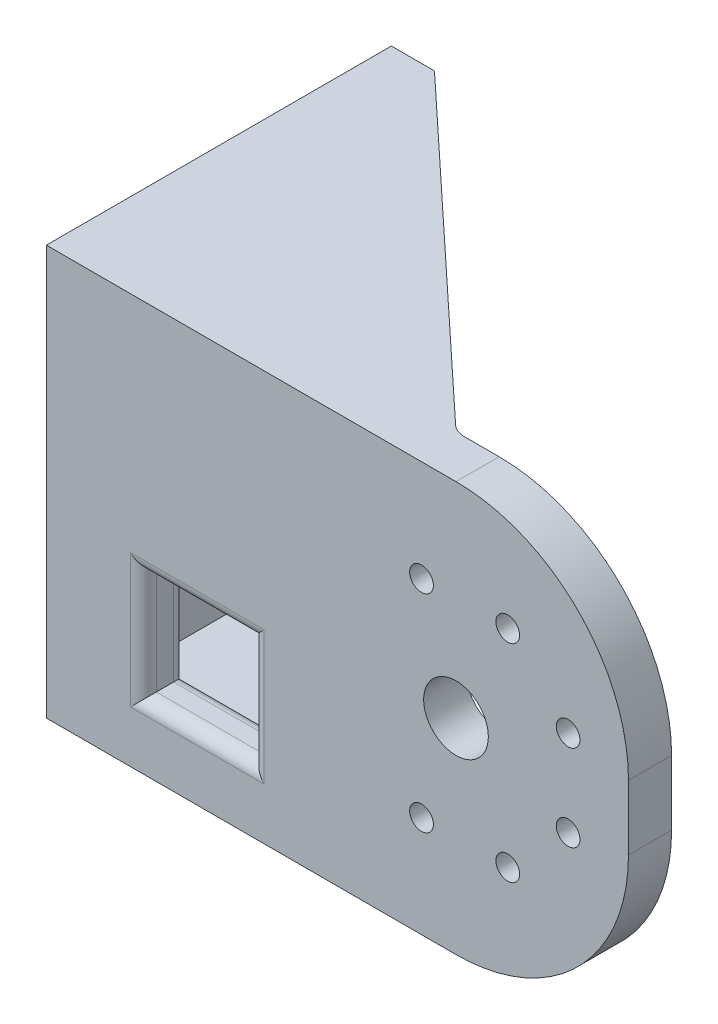
SolidWorks part; units mm, degrees
ref_plane "Front Plane" through (0, 0, 0) normal (0, 0, 1) x (1, 0, 0)
ref_plane "Top Plane" through (0, 0, 0) normal (0, 1, 0) x (1, 0, 0)
ref_plane "Right Plane" through (0, 0, 0) normal (1, 0, 0) x (0, 0, -1)
sketch "Sketch3" plane through (0, 0, 0) normal (0, 0, 1) x (1, 0, 0)
  line L6 (68.6171, 80.0599) -> (163.6171, 80.0599)
  line L10 (68.6171, 80.0599) -> (68.6171, -14.9401)
  line L36 (-101.4371, 49.8561) -> (-17.2351, 49.8561) construction
  line L70 (68.6171, -14.9401) -> (163.6171, -14.9401)
  line L71 (203.6171, 40.0599) -> (203.6171, 25.0599)
  circle A22 centre (163.6171, 32.5599) radius 7.5
  circle A23 centre (189.6171, 42.5599) radius 2.75
  circle A24 centre (155.6171, 56.5599) radius 2.75
  circle A25 centre (175.6171, 56.5599) radius 2.75
  circle A26 centre (155.6171, 8.5599) radius 2.75
  circle A27 centre (175.6171, 8.5599) radius 2.75
  circle A28 centre (189.6171, 22.5599) radius 2.75
  arc A29 (163.6171, -14.9401) -> (203.6171, 25.0599) centre (163.6171, 25.0599) ccw
  arc A30 (163.6171, 80.0599) -> (203.6171, 40.0599) centre (163.6171, 40.0599) cw
  point P23 (203.6171, 80.0599)
  dimension "D3" = 10
  dimension "D4" = 26
  dimension "D7" = 5.5
  dimension "D21" = 135
  dimension "D22" = 40
  dimension "D23" = 47.5
  dimension "D1" = 15
  dimension "D24" = 40
  dimension "D10" = 8
  dimension "D11" = 24
  dimension "D12" = 20
  dimension "D15" = 20
  dimension "D16" = 8
  dimension "D17" = 20
  dimension "D18" = 48
  dimension "D19" = 48
  dimension "D20" = 95
  dimension "D13" = 26
  dimension "D14" = 24
extrude "Boss-Extrude1" add sketch "Sketch3" along normal blind 10
sketch "Sketch4" plane through (0, 0, 0) normal (0, 0, -1) x (-1, 0, 0)
  line L0 (-68.6171, -14.9401) -> (-163.6171, -14.9401) construction
  line L1 (-68.6171, 80.0599) -> (-78.6171, 80.0599)
  line L2 (-68.6171, 80.0599) -> (-68.6171, -14.9401)
  line L3 (-68.6171, -14.9401) -> (-78.6171, -14.9401)
  line L4 (-78.6171, 80.0599) -> (-78.6171, -14.9401)
  dimension "D1" = 10
extrude "Boss-Extrude2" add sketch "Sketch4" along normal blind 70
sketch "Sketch8" plane through (68.6171, 0, 0) normal (-1, 0, 0) x (0, 0, 1)
  line L0 (10, 80.0599) -> (-70, 80.0599) construction
  line L1 (-40, 32.5599) -> (-56.1679, 25.863) construction
  line L2 (-70, 32.5599) -> (0, 32.5599) construction
  line L3 (-70, -14.9401) -> (-70, 80.0599) construction
  circle A0 centre (-40, 32.5599) radius 7.5
  circle A1 centre (-56.1679, 25.863) radius 2.75
  circle A2 centre (-56.1679, 39.2569) radius 2.75
  circle A3 centre (-46.697, 48.7278) radius 2.75
  circle A4 centre (-33.303, 48.7278) radius 2.75
  circle A5 centre (-23.8321, 39.2569) radius 2.75
  circle A6 centre (-23.8321, 25.863) radius 2.75
  circle A7 centre (-33.303, 16.392) radius 2.75
  circle A8 centre (-46.697, 16.392) radius 2.75
  point P27 (-40, 32.5599)
  dimension "D1" = 15
  dimension "D6" = 5.5
  dimension "D2" = 47.5
  dimension "D3" = 30
  dimension "D4" = 17.5
  dimension "D5" = 22.5
  dimension "D7" = 8
extrude "Cut-Extrude2" cut sketch "Sketch8" against normal blind 43.8
sketch "Sketch9" plane through (0, -14.9401, 0) normal (0, -1, 0) x (1, 0, 0)
  line L0 (78.6171, -70) -> (153.6171, 0)
  line L1 (52.25, 0) -> (-52.25, 0) construction
  line L2 (78.6171, 0) -> (163.6171, 0) construction
  line L3 (78.6171, -70) -> (78.6171, 0)
  line L4 (78.6171, 0) -> (153.6171, 0)
extrude "Boss-Extrude3" add sketch "Sketch9" against normal blind 10
ref_plane "Plane1" through (0, 32.5599, 0) normal (0, -1, 0) x (-1, 0, 0)
mirror "Mirror1" about plane through (0, 32.5599, 0) normal (0, -1, 0) of "Boss-Extrude3"
fillet "Fillet1" radius 5 2 edges at (153.6171, 75.0599, 0) (153.6171, -9.9401, 0)
sketch "Sketch11" plane through (0, 0, 0) normal (0, 0, -1) x (-1, 0, 0)
  line L0 (-78.6171, 70.0599) -> (-78.6171, -4.9401) construction
  line L1 (-91.1171, 0.0599) -> (-116.1171, 0.0599)
  line L2 (-91.1171, 0.0599) -> (-91.1171, 25.0599)
  line L3 (-91.1171, 25.0599) -> (-116.1171, 25.0599)
  line L4 (-116.1171, 0.0599) -> (-116.1171, 25.0599)
  line L5 (-155.5879, -4.9401) -> (-78.6171, -4.9401) construction
  dimension "D1" = 12.5
  dimension "D2" = 25
  dimension "D3" = 25
  dimension "D4" = 5
extrude "Cut-Extrude3" cut sketch "Sketch11" against normal through all
fillet "Fillet3" radius 3 8 edges at (116.1171, 12.5599, 0) (116.1171, 12.5599, 10) (103.6171, 0.0599, 10) (103.6171, 0.0599, 0) (91.1171, 12.5599, 10) (103.6171, 25.0599, 10) (103.6171, 25.0599, 0) (91.1171, 12.5599, 0)
